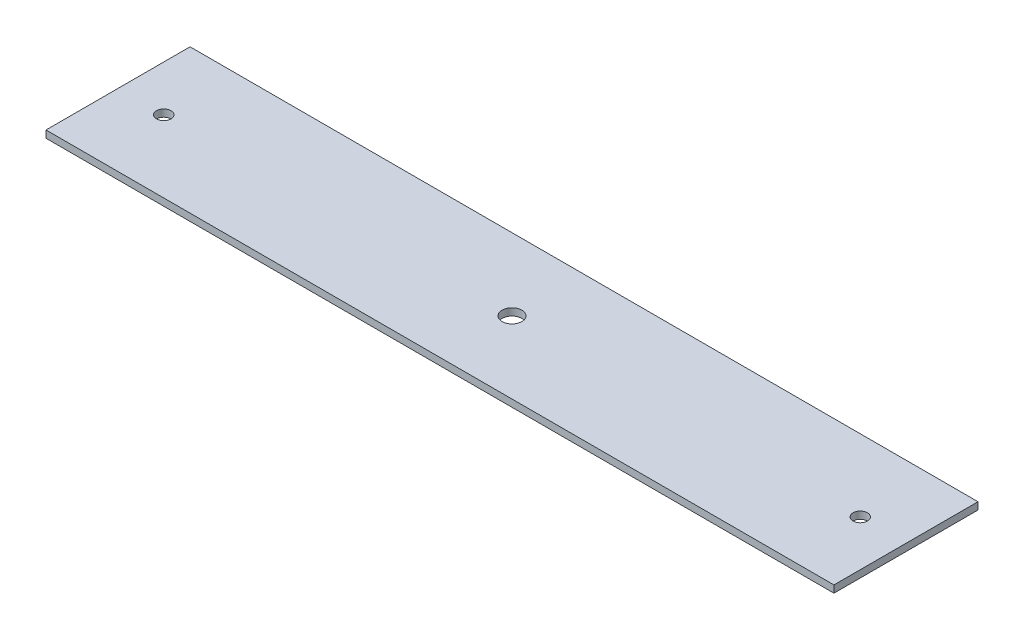
SolidWorks part; units mm, degrees
material "AISI 304"
ref_plane "Front Plane" through (0, 0, 0) normal (0, 0, 1) x (1, 0, 0)
ref_plane "Top Plane" through (0, 0, 0) normal (0, 1, 0) x (1, 0, 0)
ref_plane "Right Plane" through (0, 0, 0) normal (1, 0, 0) x (0, 0, -1)
sketch "Sketch1" plane through (0, 0, 0) normal (0, 1, 0) x (1, 0, 0)
  line L1 (218.8, 40) -> (-218.8, 40)
  line L2 (218.8, 40) -> (218.8, -40)
  line L3 (218.8, -40) -> (-218.8, -40)
  line L4 (-218.8, 40) -> (-218.8, -40)
  line L5 (218.8, 40) -> (-218.8, -40) construction
  line L6 (218.8, -40) -> (-218.8, 40) construction
  circle A0 centre (0, 0) radius 5.5
  circle A1 centre (-193.4, 0) radius 4
  circle A2 centre (193.4, 0) radius 4
  point P0 (0, 0)
  dimension "D3" = 11
  dimension "D4" = 8
  dimension "D1" = 437.6
  dimension "D2" = 80
  dimension "D5" = 25.4
  dimension "D6" = 25.4
extrude "Boss-Extrude1" add sketch "Sketch1" along normal blind 4
